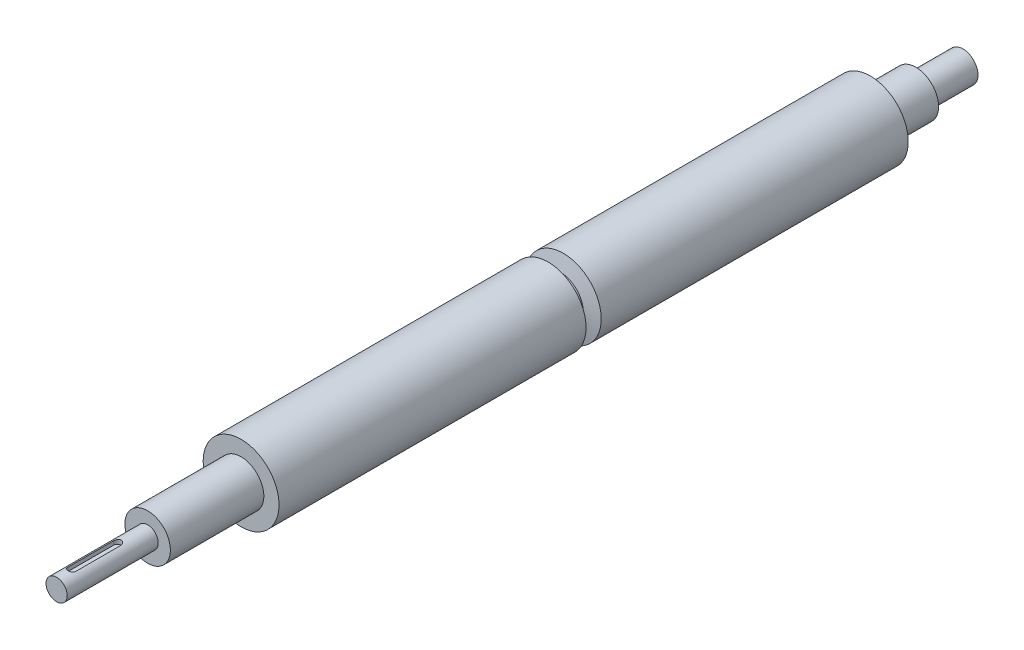
SolidWorks part; units mm, degrees
ref_plane "Plan de face" through (0, 0, 0) normal (0, 0, 1) x (1, 0, 0)
ref_plane "Plan de dessus" through (0, 0, 0) normal (0, 1, 0) x (1, 0, 0)
ref_plane "Plan de droite" through (0, 0, 0) normal (1, 0, 0) x (0, 0, -1)
sketch "Esquisse1" plane through (0, 0, 0) normal (0, 0, 1) x (1, 0, 0)
  circle A0 centre (0, 0) radius 7
  dimension "D1" = 14
extrude "Boss.-Extru.1" add sketch "Esquisse1" along normal blind 60
sketch "Esquisse2" plane through (0, 0, 0) normal (0, 0, -1) x (-1, 0, 0)
  circle A0 centre (0, 0) radius 15
  dimension "D1" = 30
extrude "Boss.-Extru.2" add sketch "Esquisse2" along normal blind 61.6
sketch "Esquisse3" plane through (0, 0, -61.6) normal (0, 0, -1) x (-1, 0, 0)
  circle A0 centre (0, 0) radius 25
extrude "Boss.-Extru.3" add sketch "Esquisse3" along normal blind 414.8
sketch "Esquisse4" plane through (0, 0, -476.4) normal (0, 0, -1) x (-1, 0, 0)
  circle A0 centre (0, 0) radius 15
  dimension "D1" = 30
extrude "Boss.-Extru.4" add sketch "Esquisse4" along normal blind 30
sketch "Esquisse5" plane through (0, 0, -506.4) normal (0, 0, -1) x (-1, 0, 0)
  circle A0 centre (0, 0) radius 10
extrude "Boss.-Extru.5" add sketch "Esquisse5" along normal blind 31
ref_plane "Plan1" through (0, 7, 0) normal (0, 1, 0) x (1, 0, 0)
sketch "Esquisse7" plane through (0, 7, 0) normal (0, 1, 0) x (1, 0, 0)
  line L0 (0, -50) -> (0, -20) construction
  line L1 (-2.5, -50) -> (-2.5, -20)
  line L2 (2.5, -50) -> (2.5, -20)
  line L3 (-7, -60) -> (7, -60) construction
  arc A0 (-2.5, -50) -> (2.5, -50) centre (0, -50) ccw
  arc A1 (2.5, -20) -> (-2.5, -20) centre (0, -20) ccw
  point P3 (0, -35)
  dimension "D1" = 10
  dimension "D2" = 30
extrude "Enlèv. mat.-Extru.1" cut sketch "Esquisse7" against normal blind 2.96
ref_plane "Plan2" through (0, 0, 0) normal (1, 0, 0) x (0, 0, -1)
sketch "Esquisse8" plane through (0, 0, 0) normal (1, 0, 0) x (0, 0, -1)
  line L0 (264, 25) -> (274, 25)
  line L1 (476.4, 25) -> (61.6, 25) construction
  line L2 (274, 25) -> (272, 15.202)
  line L3 (272, 15.202) -> (266, 15.202)
  line L4 (266, 15.202) -> (264, 25)
  line L6 (476.4, -25) -> (476.4, 25) construction
  line L7 (0, 0) -> (474.8695, 0)
  dimension "D1" = 10
  dimension "D2" = 6
  dimension "D3" = 10
  dimension "D4" = 10
  dimension "D5" = 202.4
revolve "Enlèvement de matière-Révolution1" cut sketch "Esquisse8" angle 360 about L7
